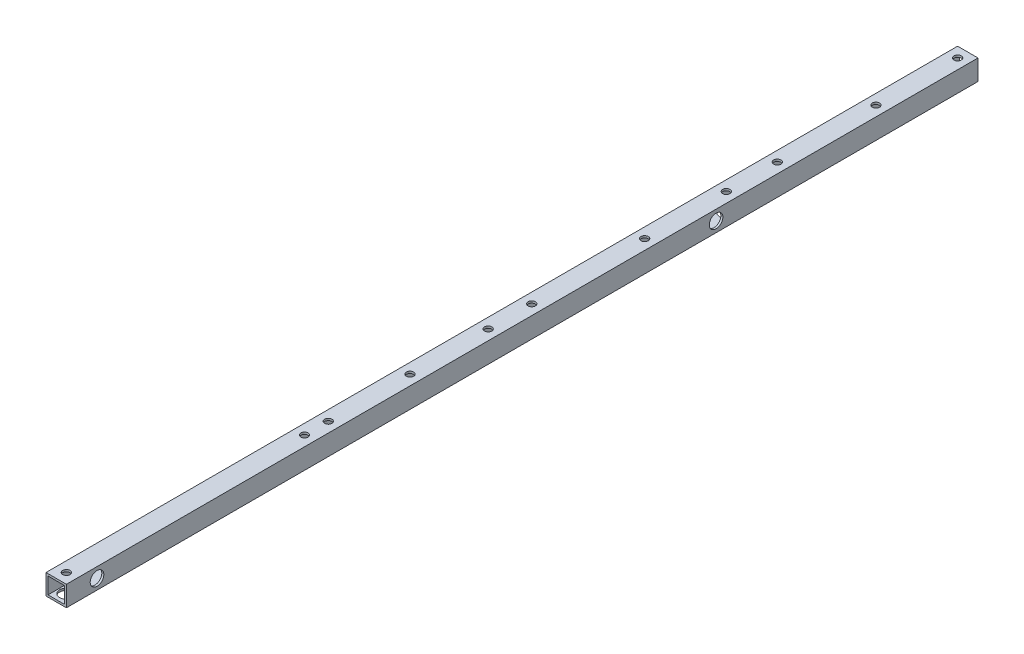
SolidWorks part; units mm, degrees
material "6063-T5"
ref_plane "正面" through (0, 0, 0) normal (0, 0, 1) x (1, 0, 0)
ref_plane "平面" through (0, 0, 0) normal (0, 1, 0) x (1, 0, 0)
ref_plane "右側面" through (0, 0, 0) normal (1, 0, 0) x (0, 0, -1)
sketch "ｽｹｯﾁ1" plane through (0, 0, 0) normal (0, 0, 1) x (1, 0, 0)
  line L1 (-7.5, -7.5) -> (7.5, -7.5)
  line L2 (-7.5, -7.5) -> (-7.5, 7.5)
  line L3 (-7.5, 7.5) -> (7.5, 7.5)
  line L4 (7.5, -7.5) -> (7.5, 7.5)
  line L5 (-7.5, -7.5) -> (7.5, 7.5) construction
  line L6 (-7.5, 7.5) -> (7.5, -7.5) construction
  line L7 (-6, -6) -> (6, -6)
  line L8 (-6, -6) -> (-6, 6)
  line L9 (-6, 6) -> (6, 6)
  line L10 (6, -6) -> (6, 6)
  line L11 (-6, -6) -> (6, 6) construction
  line L12 (-6, 6) -> (6, -6) construction
  point P0 (0, 0)
  point P6 (0, 0)
  dimension "D1" = 1.5
  dimension "D2" = 15
  dimension "D3" = 15
extrude "ﾎﾞｽ - 押し出し1" add sketch "ｽｹｯﾁ1" along normal blind 670
sketch "ｽｹｯﾁ4" plane through (7.5, 0, 0) normal (1, 0, 0) x (0, 0, -1)
  line L0 (-670, -7.5) -> (-670, 7.5) construction
  line L1 (-670, -7.5) -> (0, -7.5) construction
  circle A4 centre (-647.5, 0) radius 2.7
  circle A6 centre (-192.5, 0) radius 2.7
  dimension "D2" = 2
  dimension "D3" = 5.4
  dimension "D8" = 5.4
  dimension "D9" = 7.5
  dimension "D4" = 455
  dimension "D10" = 22.5
extrude "ｶｯﾄ - 押し出し3" cut sketch "ｽｹｯﾁ4" against normal blind 20
sketch "ｽｹｯﾁ3" plane through (0, 7.5, 0) normal (0, 1, 0) x (1, 0, 0)
  line L0 (7.5, -670) -> (-7.5, -670) construction
  line L1 (0, -662.5) -> (0, -177.5) construction
  line L2 (7.5, -670) -> (7.5, 0) construction
  circle A1 centre (0, -177.5) radius 2.7
  circle A6 centre (0, -487.5) radius 2.7
  circle A8 centre (0, -352.5) radius 2.7
  circle A9 centre (0, -662.5) radius 2.7
  circle A10 centre (0, -140) radius 2.7
  dimension "D2" = 492.5
  dimension "D3" = 5.4
  dimension "D7" = 135
  dimension "D8" = 7.5
  dimension "D9" = 7.5
  dimension "D11" = 5.4
  dimension "D4" = 7.5
  dimension "D5" = 5.4
  dimension "D12" = 182.5
  dimension "D10" = 7.5
  dimension "D13" = 37.5
  dimension "D6" = 2
extrude "ｶｯﾄ - 押し出し4" cut sketch "ｽｹｯﾁ3" against normal blind 30
sketch "ｽｹｯﾁ5" plane through (0, 7.5, 0) normal (0, 1, 0) x (1, 0, 0)
  line L0 (7.5, 0) -> (-7.5, 0) construction
  line L1 (7.5, -670) -> (7.5, 0) construction
  line L2 (7.5, -670) -> (-7.5, -670) construction
  circle A0 centre (0, -7.5) radius 2.7
  circle A1 centre (0, -67.5) radius 2.7
  circle A2 centre (0, -410) radius 2.7
  circle A3 centre (0, -470) radius 2.7
  dimension "D1" = 60
  dimension "D2" = 7.5
  dimension "D3" = 7.5
  dimension "D4" = 7.5
  dimension "D5" = 7.5
  dimension "D6" = 5.4
  dimension "D7" = 5.4
  dimension "D9" = 200
  dimension "D8" = 2
extrude "ｶｯﾄ - 押し出し5" cut sketch "ｽｹｯﾁ5" against normal blind 40
sketch "ｽｹｯﾁ6" plane through (0, -7.5, 0) normal (0, -1, 0) x (-1, 0, 0)
  circle A0 centre (0, -662.5) radius 5
  circle A1 centre (0, -177.5) radius 5
  circle A2 centre (0, -352.5) radius 5
  circle A3 centre (0, -487.5) radius 5
  circle A4 centre (0, -470) radius 5
  circle A5 centre (0, -410) radius 5
  circle A6 centre (0, -67.5) radius 5
  circle A7 centre (0, -7.5) radius 5
  circle A8 centre (0, -140) radius 5
  dimension "D1" = 10
  dimension "D2" = 10
  dimension "D3" = 10
  dimension "D4" = 10
  dimension "D5" = 2
  dimension "D6" = 2
  dimension "D7" = 2
extrude "ｶｯﾄ - 押し出し6" cut sketch "ｽｹｯﾁ6" against normal blind 10
sketch "ｽｹｯﾁ7" plane through (7.5, 0, 0) normal (1, 0, 0) x (0, 0, -1)
  circle A0 centre (-647.5, 0) radius 5
  circle A1 centre (-192.5, 0) radius 5
  dimension "D1" = 10
  dimension "D2" = 10
extrude "ｶｯﾄ - 押し出し7" cut sketch "ｽｹｯﾁ7" against normal blind 10
sketch "ｽｹｯﾁ8" plane through (0, 7.5, 0) normal (0, 1, 0) x (1, 0, 0)
  circle A0 centre (0, -177.5) radius 2.7 construction
  point P0 (0, -237.5)
  point P1 (0, -320.5)
  dimension "D2" = 60
  dimension "D1" = 83
hole_wizard "Ø5.4 (5.4) 直径の穴1" positions "ｽｹｯﾁ8" profile "ｽｹｯﾁ9" hole size "Ø5.4" standard "JIS" end condition through all
sketch "ｽｹｯﾁ9" plane through (0, 7.5, 237.5) normal (1, 0, 0) x (0, 0, 1)
  line L0 (0, 0) -> (0, 15)
  line L1 (0, 15) -> (2.7, 15)
  line L2 (2.7, 15) -> (2.7, 0)
  line L5 (2.7, 0) -> (0, 0)
  line L11 (0, -6.35) -> (0, 107.95) construction
  dimension "通し穴の直径" = 5.4
  dimension "通し穴の深さ" = 15
hole_wizard "Ø10.0 (10) 直径の穴1" positions "ｽｹｯﾁ10" profile "ｽｹｯﾁ11" hole size "Ø10.0" standard "JIS"
sketch "ｽｹｯﾁ10" plane through (0, -7.5, 0) normal (0, -1, 0) x (-1, 0, 0)
  point P0 (0, -237.5)
  point P3 (0, -320.5)
sketch "ｽｹｯﾁ11" plane through (0, -7.5, 237.5) normal (1, 0, 0) x (0, 0, -1)
  line L0 (0, 0) -> (0, 4.5043)
  line L1 (0, 4.5043) -> (5, 1.5)
  line L2 (5, 1.5) -> (5, 0)
  line L5 (5, 0) -> (0, 0)
  line L10 (0, 4.5043) -> (-5, 1.5) construction
  line L11 (0, -6.35) -> (0, 107.95) construction
  dimension "穴の直径" = 10
  dimension "穴の深さ" = 1.5
  dimension "ﾄﾞﾘﾙ角度" = 118
